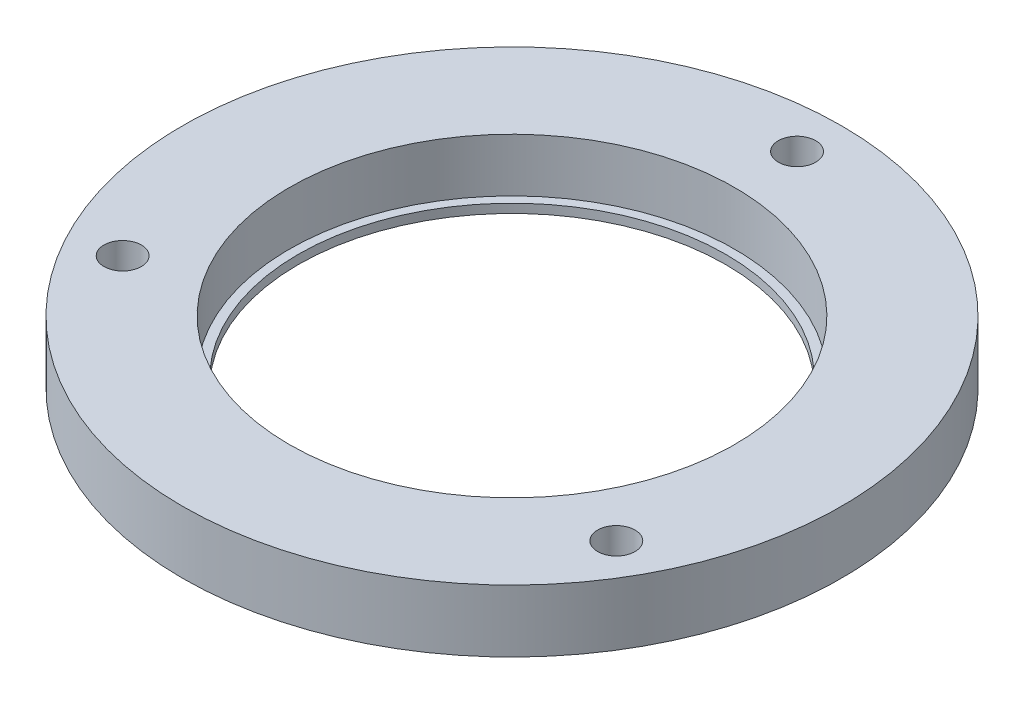
SolidWorks part; units mm, degrees
ref_plane "Front Plane" through (0, 0, 0) normal (0, 0, 1) x (1, 0, 0)
ref_plane "Top Plane" through (0, 0, 0) normal (0, 1, 0) x (1, 0, 0)
ref_plane "Right Plane" through (0, 0, 0) normal (1, 0, 0) x (0, 0, -1)
sketch "Sketch1" plane through (0, 0, 0) normal (0, 1, 0) x (1, 0, 0)
  circle A0 centre (0, 0) radius 37
  dimension "D1" = 74
extrude "Boss-Extrude1" add sketch "Sketch1" along normal blind 6
sketch "Sketch2" plane through (0, 6, 0) normal (0, 1, 0) x (1, 0, 0)
  circle A0 centre (0, 32) radius 2.1
  point P2 (0, 0)
  dimension "D1" = 4.2
  dimension "D2" = 32
extrude "Cut-Extrude1" cut sketch "Sketch2" against normal through all
pattern_circular "CirPattern1" count 3 over 360 about axis through (0, 0, 0) along (0, 1, 0) of "Cut-Extrude1"
sketch "Sketch3" plane through (0, 6, 0) normal (0, 1, 0) x (1, 0, 0)
  circle A0 centre (0, 0) radius 25
  dimension "D1" = 50
extrude "Cut-Extrude2" cut sketch "Sketch3" against normal through all
sketch "Sketch4" plane through (0, 0, 0) normal (0, 1, 0) x (1, 0, 0)
  circle A0 centre (0, 0) radius 37
  circle A1 centre (0, 0) radius 24
  circle A2 centre (0, 0) radius 37 construction
  circle A3 centre (0, 0) radius 25 construction
  circle A4 centre (-27.7128, -16) radius 2.1 construction
  circle A5 centre (27.7128, -16) radius 2.1 construction
  circle A6 centre (0, 32) radius 2.1 construction
  circle A7 centre (-27.7128, -16) radius 2.1
  circle A8 centre (27.7128, -16) radius 2.1
  circle A9 centre (0, 32) radius 2.1
  dimension "D1" = 1
extrude "Boss-Extrude2" add sketch "Sketch4" against normal blind 1
